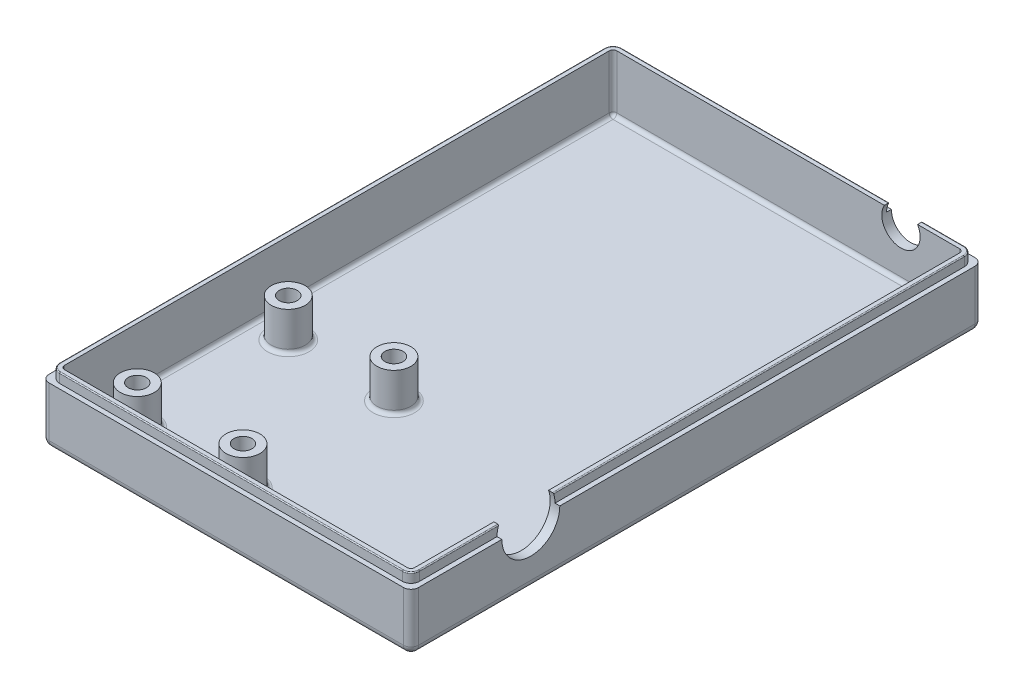
SolidWorks part; units mm, degrees
ref_plane "Front Plane" through (0, 0, 0) normal (0, 0, 1) x (1, 0, 0)
ref_plane "Top Plane" through (0, 0, 0) normal (0, 1, 0) x (1, 0, 0)
ref_plane "Right Plane" through (0, 0, 0) normal (1, 0, 0) x (0, 0, -1)
sketch "Sketch1" plane through (0, 0, 0) normal (0, 1, 0) x (1, 0, 0)
  line L6 (-48.9411, -75.7074) -> (-48.9411, 75.7074)
  line L8 (48.9411, -75.7074) -> (-48.9411, -75.7074)
  line L11 (-40.8078, -24.8241) -> (-35.5508, -29.3788)
  line L12 (-9.8611, -61.423) -> (-37.8611, -61.423) construction
  line L18 (-34.9144, -18.022) -> (-29.6574, -22.5767)
  line L20 (-37.8611, -21.423) -> (-9.8611, -21.423) construction
  line L23 (-48.9411, 75.7074) -> (48.9411, 75.7074)
  line L25 (-37.8611, -61.423) -> (-37.8611, -21.423) construction
  line L26 (48.9411, -75.7074) -> (48.9411, 75.7074)
  line L29 (-9.8611, -21.423) -> (-9.8611, -61.423) construction
  circle A11 centre (-9.8611, -61.423) radius 4.5
  circle A12 centre (-37.8611, -61.423) radius 4.5
  arc A22 (-40.8078, -24.8241) -> (-34.9144, -18.022) centre (-37.8611, -21.423) cw
  arc A23 (-29.6574, -22.5767) -> (-35.5508, -29.3788) centre (-32.6041, -25.9777) cw
  circle A24 centre (-9.8611, -21.423) radius 4.5
  circle A31 centre (-37.8611, -21.423) radius 4.5 construction
  circle A32 centre (-32.6041, -25.9777) radius 4.5 construction
  point P1 (0, -75.7074)
  point P2 (-48.9411, 0)
  dimension "D7" = 97.8822
  dimension "D10" = 11.08
  dimension "D19" = 5.257
  dimension "D32" = 9
  dimension "D35" = 9
  dimension "D36" = 9
  dimension "D5" = 97.1304
  dimension "D6" = 58.8022
  dimension "D2" = 6.9557
  dimension "D4" = 54.2843
  dimension "D15" = 40
  dimension "D16" = 28
extrude "Boss-Extrude1" add sketch "Sketch1" along normal mid plane 2.54
sketch "Sketch2" plane through (0, 1.27, 0) normal (0, 1, 0) x (1, 0, 0)
  line L0 (-46.4011, 73.1674) -> (-46.4011, -73.1674)
  line L1 (-46.4011, -73.1674) -> (46.4011, -73.1674)
  line L2 (46.4011, -73.1674) -> (46.4011, 73.1674)
  line L3 (46.4011, 73.1674) -> (-46.4011, 73.1674)
  line L4 (48.9411, 75.7074) -> (-48.9411, 75.7074)
  line L5 (-48.9411, 75.7074) -> (-48.9411, -75.7074)
  line L6 (-48.9411, -75.7074) -> (48.9411, -75.7074)
  line L7 (48.9411, -75.7074) -> (48.9411, 75.7074)
  line L8 (48.9411, 75.7074) -> (-48.9411, 75.7074)
  line L9 (-48.9411, 75.7074) -> (-48.9411, -75.7074)
  line L10 (-48.9411, -75.7074) -> (48.9411, -75.7074)
  line L11 (48.9411, -75.7074) -> (48.9411, 75.7074)
  dimension "D1" = 2.54
  dimension "D4" = 0
extrude "Boss-Extrude2" add sketch "Sketch2" along normal blind 12.7
sketch "Sketch4" plane through (0, 1.27, 0) normal (0, 1, 0) x (1, 0, 0)
  line L2 (-40.8078, -24.8241) -> (-35.5508, -29.3788)
  line L3 (-29.6574, -22.5767) -> (-34.9144, -18.022)
  circle A1 centre (-9.8611, -21.423) radius 4.5
  circle A2 centre (-9.8611, -21.423) radius 4.5
  circle A3 centre (-37.8611, -61.423) radius 4.5
  circle A4 centre (-37.8611, -61.423) radius 4.5
  circle A5 centre (-9.8611, -61.423) radius 4.5
  circle A6 centre (-9.8611, -61.423) radius 4.5
  arc A8 (-34.9144, -18.022) -> (-40.8078, -24.8241) centre (-37.8611, -21.423) ccw
  arc A9 (-35.5508, -29.3788) -> (-29.6574, -22.5767) centre (-32.6041, -25.9777) ccw
  circle A10 centre (-37.8611, -21.423) radius 4.5
  point P0 (-40.0937, -24.8241)
  dimension "D1" = 0
  dimension "D2" = 0
  dimension "D3" = 0
  dimension "D5" = 0
extrude "Boss-Extrude3" add sketch "Sketch4" along normal blind 10.16
fillet "Fillet1" radius 2 8 edges at (-48.9411, -1.27, 0) (0, -1.27, 75.7074) (48.9411, -1.27, 0) (-48.9411, 6.35, 75.7074) (-48.9411, 6.35, -75.7074) (48.9411, 6.35, -75.7074) (48.9411, 6.35, 75.7074) (0, -1.27, -75.7074)
fillet "Fillet2" radius 1 8 edges at (46.4011, 7.62, 73.1674) (-46.4011, 7.62, 73.1674) (-46.4011, 7.62, -73.1674) (46.4011, 1.27, 0) (46.4011, 7.62, -73.1674) (0, 1.27, -73.1674) (0, 1.27, 73.1674) (-46.4011, 1.27, 0)
fillet "Fillet3" radius 1 4 edges at (-37.8611, 1.27, 25.923) (-37.8611, 1.27, 65.923) (-9.8611, 1.27, 65.923) (-9.8611, 1.27, 25.923)
sketch "Sketch5" plane through (0, 11.43, 0) normal (0, 1, 0) x (1, 0, 0)
  point P0 (-37.8611, -21.423)
  point P3 (-37.8611, -61.423)
  point P6 (-9.8611, -21.423)
  point P9 (-9.8611, -61.423)
hole_wizard "3/16 (0.1875) Diameter Hole1" positions "Sketch5" profile "Sketch6" hole size "3/16" standard "ANSI Inch"
sketch "Sketch6" plane through (-37.8611, 11.43, 21.423) normal (1, 0, 0) x (0, 0, 1)
  line L0 (0, 0) -> (0, 21.4968)
  line L1 (0, 21.4968) -> (2.3812, 20.066)
  line L2 (2.3812, 20.066) -> (2.3812, 0)
  line L5 (2.3812, 0) -> (0, 0)
  line L10 (0, 21.4968) -> (-2.3812, 20.066) construction
  line L11 (0, -6.35) -> (0, 107.95) construction
  dimension "Hole Dia." = 4.7625
  dimension "Hole Depth" = 20.066
  dimension "Drill Angle" = 118
sketch "Sketch7" plane through (0, 13.97, 0) normal (0, 1, 0) x (1, 0, 0)
  line L0 (46.4011, 72.1674) -> (46.4011, -72.1674) construction
  line L1 (-45.4011, 73.1674) -> (45.4011, 73.1674) construction
  line L2 (-46.4011, -72.1674) -> (-46.4011, 72.1674) construction
  line L3 (45.4011, -73.1674) -> (-45.4011, -73.1674) construction
  line L4 (46.4011, 72.1674) -> (46.4011, -72.1674)
  line L5 (-45.4011, 73.1674) -> (45.4011, 73.1674)
  line L6 (-46.4011, -72.1674) -> (-46.4011, 72.1674)
  line L7 (45.4011, -73.1674) -> (-45.4011, -73.1674)
  line L8 (45.4011, -74.4374) -> (-45.4011, -74.4374)
  line L9 (-47.6711, -72.1674) -> (-47.6711, 72.1674)
  line L10 (-45.4011, 74.4374) -> (45.4011, 74.4374)
  line L11 (47.6711, 72.1674) -> (47.6711, -72.1674)
  arc A0 (45.4011, -73.1674) -> (46.4011, -72.1674) centre (45.4011, -72.1674) ccw construction
  arc A1 (46.4011, 72.1674) -> (45.4011, 73.1674) centre (45.4011, 72.1674) ccw construction
  arc A2 (-45.4011, 73.1674) -> (-46.4011, 72.1674) centre (-45.4011, 72.1674) ccw construction
  arc A3 (-46.4011, -72.1674) -> (-45.4011, -73.1674) centre (-45.4011, -72.1674) ccw construction
  arc A4 (45.4011, -73.1674) -> (46.4011, -72.1674) centre (45.4011, -72.1674) ccw
  arc A5 (46.4011, 72.1674) -> (45.4011, 73.1674) centre (45.4011, 72.1674) ccw
  arc A6 (-45.4011, 73.1674) -> (-46.4011, 72.1674) centre (-45.4011, 72.1674) ccw
  arc A7 (-46.4011, -72.1674) -> (-45.4011, -73.1674) centre (-45.4011, -72.1674) ccw
  arc A8 (-47.6711, -72.1674) -> (-45.4011, -74.4374) centre (-45.4011, -72.1674) ccw
  arc A9 (-45.4011, 74.4374) -> (-47.6711, 72.1674) centre (-45.4011, 72.1674) ccw
  arc A10 (47.6711, 72.1674) -> (45.4011, 74.4374) centre (45.4011, 72.1674) ccw
  arc A11 (45.4011, -74.4374) -> (47.6711, -72.1674) centre (45.4011, -72.1674) ccw
  dimension "D1" = 1.27
extrude "Boss-Extrude4" add sketch "Sketch7" along normal blind 2.54
fillet "Fillet4" radius 0.254 8 edges at (47.6711, 16.51, 0) (47.0062, 16.51, 73.7725) (0, 16.51, 74.4374) (-47.0062, 16.51, 73.7725) (-47.6711, 16.51, 0) (-47.0062, 16.51, -73.7725) (0, 16.51, -74.4374) (47.0062, 16.51, -73.7725)
sketch "Sketch8" plane through (48.9411, 0, 0) normal (1, 0, 0) x (0, 0, -1)
  line L0 (-72.1674, 13.97) -> (72.1674, 13.97) construction
  line L1 (-75.7074, 0.73) -> (-75.7074, 13.97) construction
  circle A0 centre (-43.9574, 13.97) radius 7.6835
  dimension "D1" = 15.367
  dimension "D2" = 31.75
extrude "Cut-Extrude1" cut sketch "Sketch8" against normal up to surface (2.54 mm away) up to face at (46.4011, 9.39, 0)
sketch "Sketch10" plane through (0, 0, -75.7074) normal (0, 0, -1) x (-1, 0, 0)
  line L0 (-46.9411, 13.97) -> (46.9411, 13.97) construction
  line L1 (-48.9411, 0.73) -> (-48.9411, 13.97) construction
  circle A0 centre (-29.8911, 13.97) radius 5.08
  dimension "D1" = 10.16
  dimension "D2" = 19.05
extrude "Cut-Extrude2" cut sketch "Sketch10" against normal up to next
equation "\"0.15n\"=0.122194"
